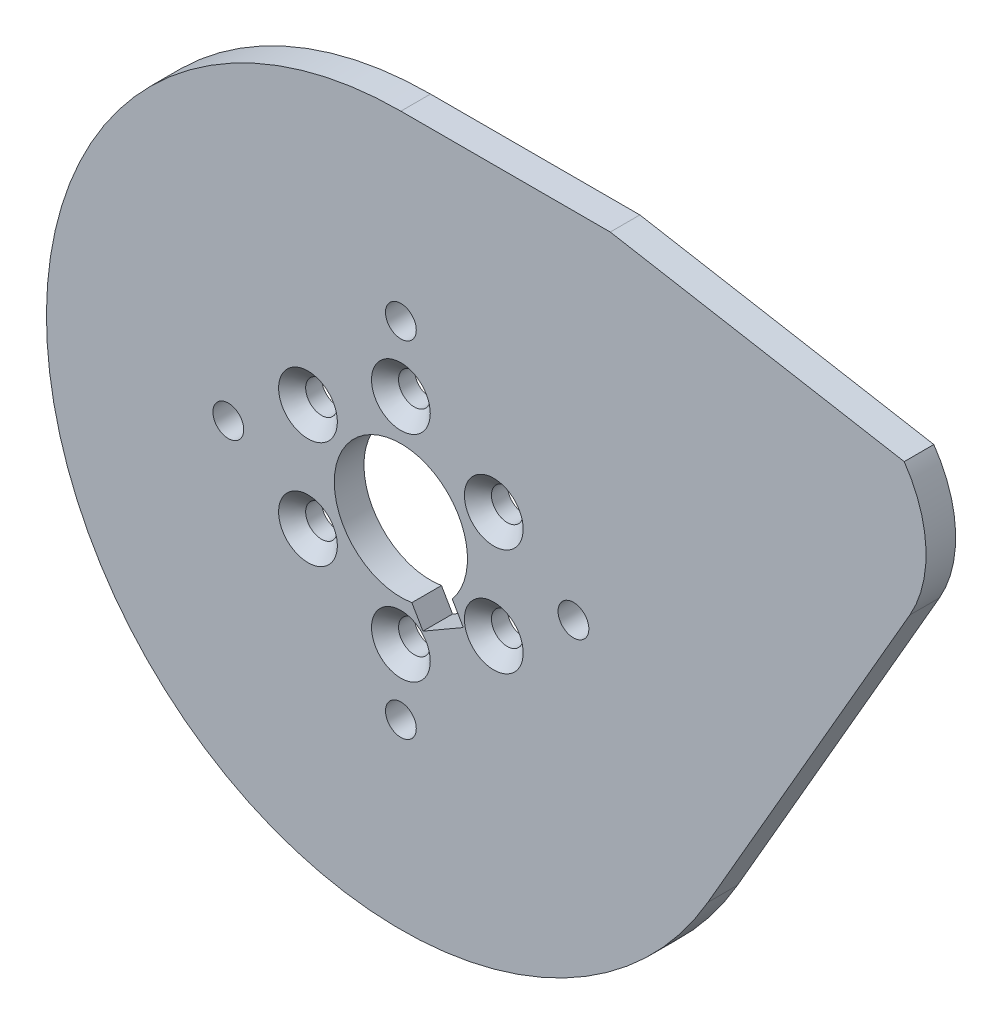
SolidWorks part; units mm, degrees
ref_plane "Front Plane" through (0, 0, 0) normal (0, 0, 1) x (1, 0, 0)
ref_plane "Top Plane" through (0, 0, 0) normal (0, 1, 0) x (1, 0, 0)
ref_plane "Right Plane" through (0, 0, 0) normal (1, 0, 0) x (0, 0, -1)
ref_plane "Plane1" through (0, 0, 3.175) normal (0, 0, 1) x (1, 0, 0)
sketch "Sketch1" plane through (0, 0, 3.175) normal (0, 0, 1) x (1, 0, 0)
  line L0 (53.9595, 32.4433) -> (22.4457, 38)
  line L1 (22.4457, 38) -> (0, 38)
  line L2 (32.909, -19) -> (54.5596, 18.5)
  arc A0 (54.5596, 18.5) -> (53.9595, 32.4433) centre (43.3013, 25) ccw
  arc A1 (0, 38) -> (32.909, -19) centre (0, 0) ccw
extrude "Boss-Extrude1" add sketch "Sketch1" against normal blind 3.175
sketch "Sketch3" plane through (0, 0, 3.175) normal (0, 0, 1) x (1, 0, 0)
  line L0 (37.0091, 35.4321) -> (53.9595, 32.4433)
  line L1 (53.6014, 19.292) -> (36.1984, 33.6765)
  arc A0 (36.1984, 33.6765) -> (37.0091, 35.4321) centre (36.8355, 34.4473) cw
  arc A1 (53.9595, 32.4433) -> (55.15, 19.6513) centre (43.3013, 25) cw
  arc A2 (55.15, 19.6513) -> (53.6014, 19.292) centre (54.2385, 20.0628) cw
ref_plane "Plane2" through (0, 0, 0) normal (0, -1, 0) x (1, 0, 0)
sketch "Sketch4" plane through (0, 0, 0) normal (0, -1, 0) x (1, 0, 0)
  line L0 (7.1374, 3.175) -> (0, 3.175)
  line L1 (0, 3.175) -> (0, 0)
  line L2 (0, 0) -> (7.1374, 0)
  line L3 (7.1374, 0) -> (7.1374, 3.175)
  line L4 (0, 3.175) -> (0, 0) construction
  dimension "D1" = 7.1374
revolve "Cut-Revolve1" cut sketch "Sketch4" angle 360 about L4
hole_wizard "#4 Clearance Hole1" positions "Sketch6" profile "Sketch5" hole size "#4" standard "ANSI Inch"
sketch "Sketch6" plane through (0, 0, 3.175) normal (0, 0, 1) x (1, 0, 0)
  point P0 (18.5, 0)
  point P1 (0, -18.5)
  point P2 (-18.5, 0)
  point P3 (0, 18.5)
sketch "Sketch5" plane through (18.5, 0, 3.175) normal (1, 0, 0) x (0, -1, 0)
  line L0 (0, 0) -> (0, 3.175)
  line L1 (0, 3.175) -> (1.65, 3.175)
  line L2 (1.65, 3.175) -> (1.65, 0)
  line L5 (1.65, 0) -> (0, 0)
  line L11 (0, -6.35) -> (0, 107.95) construction
  dimension "Thru Hole Dia." = 3.3
  dimension "Thru Hole Depth" = 3.175
hole_wizard "CSK for #4 Flat Head Machine Screw (100)1" positions "Sketch8" profile "Sketch7" countersink size "#4" standard "ANSI Inch"
sketch "Sketch8" plane through (0, 0, 3.175) normal (0, 0, 1) x (1, 0, 0)
  point P0 (-9.9593, 5.75)
  point P1 (-9.9593, -5.75)
  point P2 (0, -11.5)
  point P3 (9.9593, -5.75)
  point P4 (9.9593, 5.75)
  point P5 (0, 11.5)
sketch "Sketch7" plane through (-9.9593, 5.75, 3.175) normal (1, 0, 0) x (0, -1, 0)
  line L0 (0, 0) -> (0, 3.175)
  line L1 (0, 3.175) -> (1.7, 3.175)
  line L2 (1.7, 3.175) -> (1.7, 1.45)
  line L3 (1.7, 1.45) -> (3.15, 0)
  line L5 (3.15, 0) -> (0, 0)
  line L6 (-1.7, 1.45) -> (-3.15, 0) construction
  line L11 (0, -6.35) -> (0, 107.95) construction
  dimension "Thru Hole Dia." = 3.4
  dimension "Thru Hole Depth" = 3.175
  dimension "Near C'Sink Dia." = 6.3
  dimension "Near C'Sink Angle" = 90
sketch "Sketch9" plane through (0, 0, 0) normal (0, 0, -1) x (-1, 0, 0)
  line L0 (-2.3642, -9.0949) -> (-6.6943, -6.5949)
  line L1 (-6.6943, -6.5949) -> (-5.4398, -4.422)
  line L2 (-5.4398, -4.422) -> (-1.1097, -6.922)
  line L3 (-1.1097, -6.922) -> (-2.3642, -9.0949)
extrude "Cut-Extrude1" cut sketch "Sketch9" against normal through all
